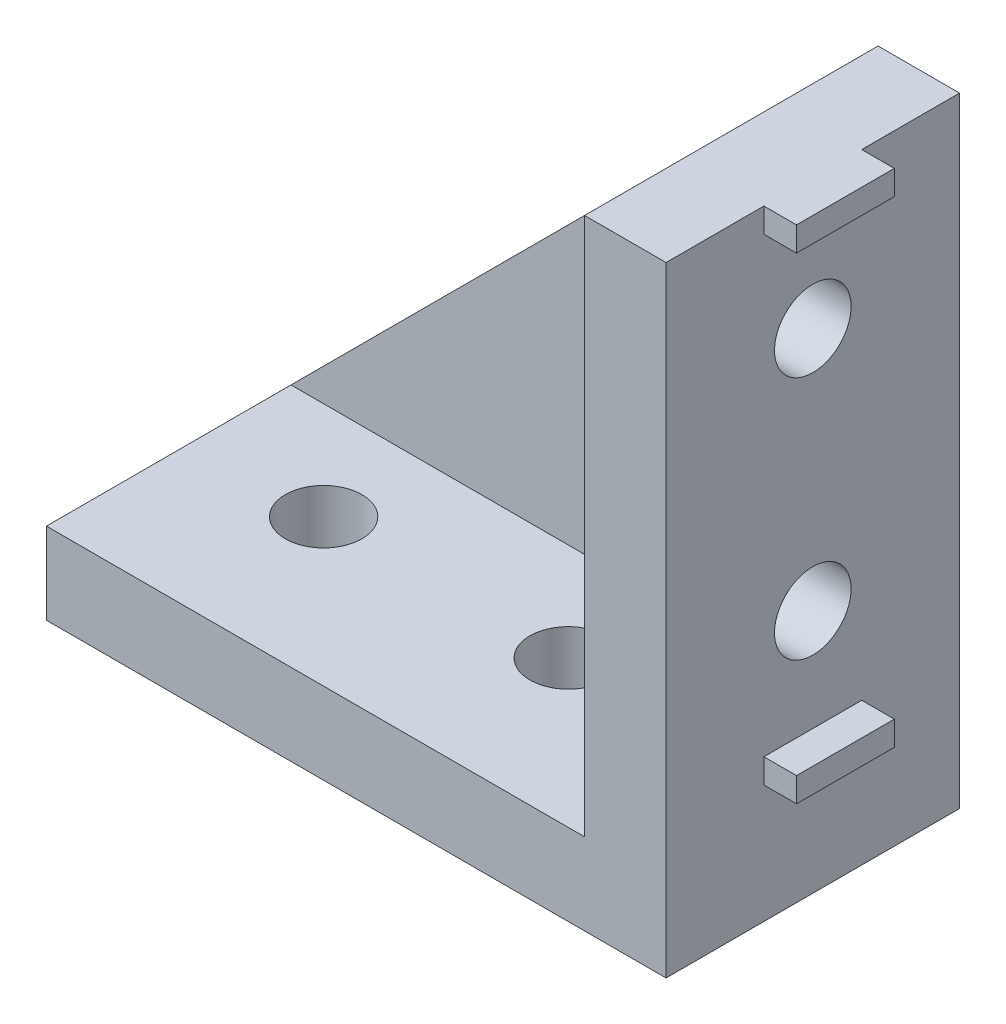
SolidWorks part; units mm, degrees
ref_plane "Front Plane" through (0, 0, 0) normal (0, 0, 1) x (1, 0, 0)
ref_plane "Top Plane" through (0, 0, 0) normal (0, 1, 0) x (1, 0, 0)
ref_plane "Right Plane" through (0, 0, 0) normal (1, 0, 0) x (0, 0, -1)
sketch "Sketch1" plane through (0, 0, 0) normal (0, 0, 1) x (1, 0, 0)
  line L0 (0, 0) -> (-38, 0)
  line L1 (-38, 0) -> (-38, 5)
  line L2 (-38, 5) -> (-5, 5)
  line L3 (-5, 5) -> (-5, 38)
  line L4 (-5, 38) -> (0, 38)
  line L5 (0, 38) -> (0, 0)
  dimension "D1" = 5
  dimension "D2" = 5
  dimension "D3" = 38
extrude "Boss-Extrude1" add sketch "Sketch1" along normal blind 18
sketch "Sketch2" plane through (0, 5, 0) normal (0, 1, 0) x (1, 0, 0)
  line L0 (-5, -9) -> (-38, -9) construction
  line L1 (-5, -18) -> (-5, 0) construction
  line L2 (-38, -18) -> (-38, 0) construction
  circle A0 centre (-30, -9) radius 2.35
  circle A1 centre (-15, -9) radius 2.35
  dimension "D1" = 4.7
  dimension "D2" = 8
  dimension "D3" = 15
extrude "Cut-Extrude1" cut sketch "Sketch2" against normal blind 18
sketch "Sketch4" plane through (0, 0, 0) normal (0, -1, 0) x (1, 0, 0)
  line L0 (-38, 9) -> (0, 9) construction
  line L1 (-38, 18) -> (-38, 0) construction
  line L2 (0, 18) -> (0, 0) construction
  line L4 (-38, 6) -> (-36.5, 6)
  line L5 (-38, 6) -> (-38, 12)
  line L6 (-38, 12) -> (-36.5, 12)
  line L7 (-36.5, 6) -> (-36.5, 12)
  line L8 (-38, 6) -> (-36.5, 12) construction
  line L9 (-38, 12) -> (-36.5, 6) construction
  line L10 (-8.75, 6) -> (-7.25, 6)
  line L11 (-8.75, 6) -> (-8.75, 12)
  line L12 (-8.75, 12) -> (-7.25, 12)
  line L13 (-7.25, 6) -> (-7.25, 12)
  line L14 (-8.75, 6) -> (-7.25, 12) construction
  line L15 (-8.75, 12) -> (-7.25, 6) construction
  point P6 (-37.25, 9)
  point P11 (-8, 9)
  dimension "D1" = 6
  dimension "D2" = 1.5
  dimension "D3" = 30
extrude "Boss-Extrude3" add sketch "Sketch4" along normal blind 2
ref_plane "Plane1" through (0, 0, 0) normal (0.7071, 0.7071, 0) x (0.7071, -0.7071, 0)
mirror "Mirror1" about plane through (0, 0, 0) normal (0.7071, 0.7071, 0) of "Boss-Extrude3", "Cut-Extrude1"
sketch "Sketch3" plane through (0, 0, 0) normal (0, 0, -1) x (-1, 0, 0)
  line L0 (5, 38) -> (38, 5)
  line L1 (38, 5) -> (5, 5)
  line L2 (5, 5) -> (38, 5) construction
  line L3 (5, 38) -> (5, 5) construction
  line L4 (5, 5) -> (5, 38)
extrude "Boss-Extrude2" add sketch "Sketch3" against normal blind 3
ref_plane "Plane2" through (0, 0, -1) normal (0, 0, -1) x (-1, 0, 0)
